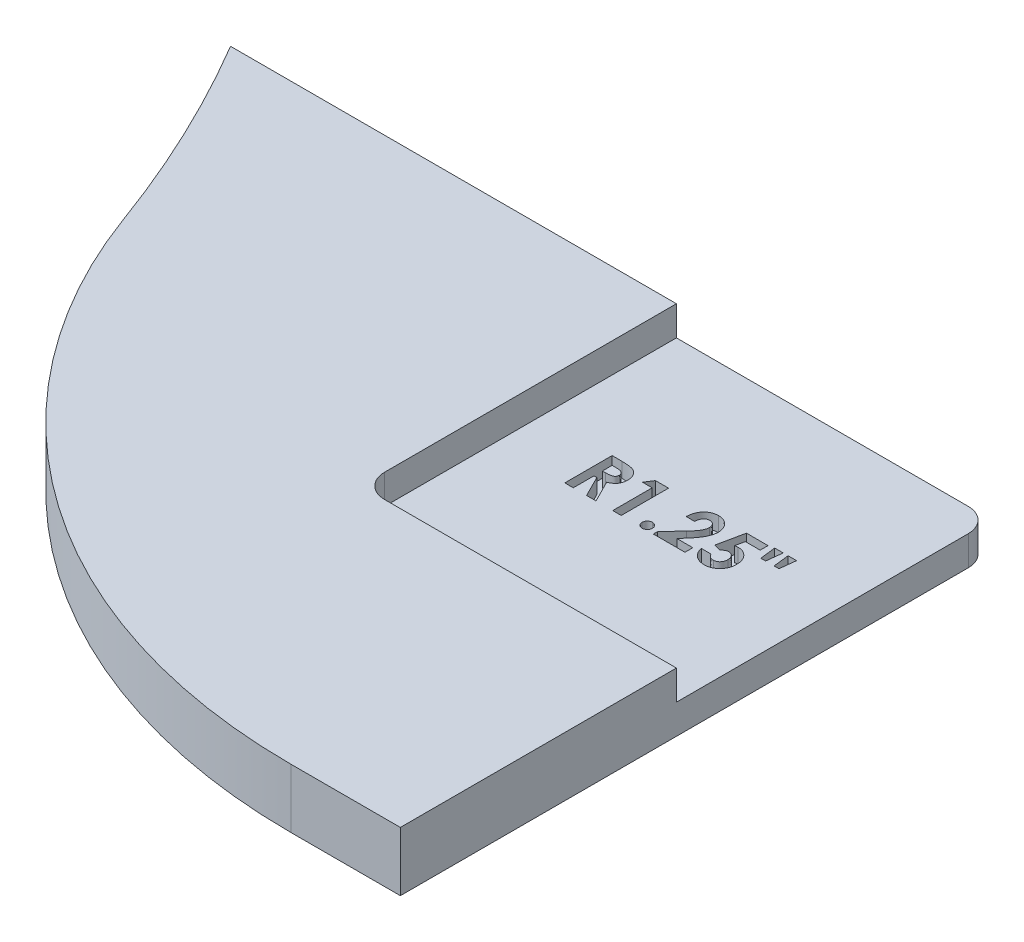
SolidWorks part; units mm, degrees
ref_plane "Front Plane" through (0, 0, 0) normal (0, 0, 1) x (1, 0, 0)
ref_plane "Top Plane" through (0, 0, 0) normal (0, 1, 0) x (1, 0, 0)
ref_plane "Right Plane" through (0, 0, 0) normal (1, 0, 0) x (0, 0, -1)
sketch "Sketch2" plane through (0, 0, 0) normal (0, 1, 0) x (1, 0, 0)
  line L0 (39.9034, 0) -> (66.5271, 0) construction
  line L4 (65.3857, 1.5875) -> (97.1357, 1.5875)
  line L5 (97.1357, 1.5875) -> (97.1357, 33.3375)
  line L6 (97.1357, 33.3375) -> (56.271, 33.3375)
  arc A0 (65.3857, 1.5875) -> (56.271, 33.3375) centre (0, 0) ccw
  arc A1 (56.271, 33.3375) -> (-65.405, 0) centre (0, 0) ccw construction
  arc A2 (-65.405, 0) -> (65.405, 0) centre (0, 0) ccw construction
  arc A3 (65.405, 0) -> (65.3857, 1.5875) centre (0, 0) ccw construction
extrude "Boss-Extrude1" add sketch "Sketch2" along normal mid plane 3.175
fillet "Fillet1" radius 31.75 1 edges at (65.3857, 0, -1.5875)
sketch "Sketch3" plane through (0, 1.5875, 0) normal (0, 1, 0) x (1, 0, 0)
  line L1 (97.1357, 33.3375) -> (80.2024, 33.3375)
  line L2 (97.1357, 33.3375) -> (97.1357, 16.4042)
  line L3 (97.1357, 16.4042) -> (80.2024, 16.4042)
  line L4 (80.2024, 33.3375) -> (80.2024, 16.4042)
  dimension "D1" = 16.9333
extrude "Cut-Extrude1" cut sketch "Sketch3" against normal blind 1.5875
sketch "Sketch4" plane through (0, 0, 0) normal (0, 1, 0) x (1, 0, 0)
  line L0 (80.2024, 24.8708) -> (97.1357, 24.8708) construction
  line L1 (80.2024, 33.3375) -> (80.2024, 16.4042) construction
  line L2 (97.1357, 16.4042) -> (97.1357, 33.3375) construction
  line L3 (80.2024, 23.6008) -> (97.1357, 23.6008) construction
  text T0 "<b>R1.25\"</b>\r\n<b> </b>" font "Century Gothic" height 2.54
  dimension "D1" = 1.27
extrude "Cut-Extrude2" cut sketch "Sketch4" against normal blind 0.7937
fillet "Fillet2" radius 1.27 2 edges at (80.2024, 0.7937, -16.4042) (97.1357, -0.7937, -33.3375)
equation "\"AIRFRAME_OD\"= 5.15in"
equation "\"AIRFRAME_ID\"= 4.99in"
equation "\"FLAT_T\"= 0.125in"
equation "\"NOSE_EXP_L\"= 27in"
equation "\"NOSE_SHOULDER_L\"= 5in"
equation "\"MAIN_L\"= 30in"
equation "\"RECO_COUP_L\"= 10in"
equation "\"RECO_SWITCH_L\"= 2in"
equation "\"DROGUE_L\"= 20in"
equation "\"ATS_FORE_COUP_L\"= 5.5in"
equation "\"ATS_AFT_COUP_L\"= 4.5in"
equation "\"LOWER_L\"= 30in"
equation "\"FIN_N\"= 4"
equation "\"CR_AFT_X\"= 0.5in"
equation "\"CR_FORE_X\"= 9.25in"
equation "\"D1@Sketch2\"=\"AIRFRAME_OD\""
equation "\"D2@Sketch2\"=\"FLAT_T\"/2"
equation "\"D1@Boss-Extrude1\"=\"FLAT_T\""
equation "\"COUPLER_OD\"= 4.998in"
equation "\"COUPLER_ID\"= 4.85in"
equation "\"RECO_ROD_X\"= 3.5in"
equation "\"ATS_ROD_X\"= 3.75in"
equation "\"FIN_ROOT\"= 8in"
equation "\"FIN_X\"= 0.75in"
equation "\"MOTOR_OD\"= 3.091in"
equation "\"MOTOR_ID\"= 3.00in"
equation "\"MOTOR_L\"= 14in"
equation "\"MOTOR_LOWER_X\"= 2in"
